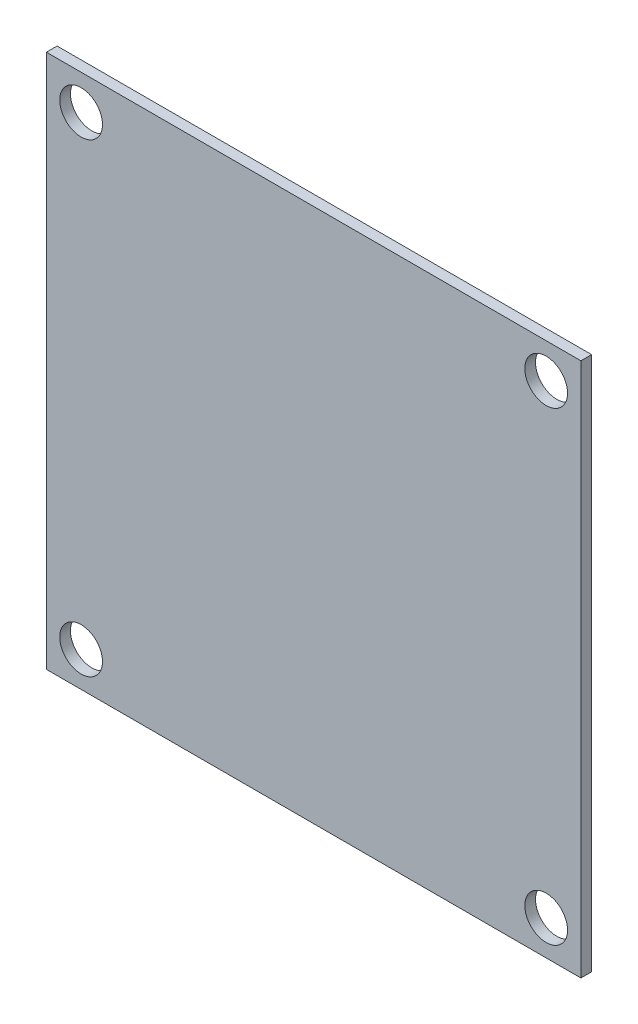
SolidWorks part; units mm, degrees
ref_plane "Front Plane" through (0, 0, 0) normal (0, 0, 1) x (1, 0, 0)
ref_plane "Top Plane" through (0, 0, 0) normal (0, 1, 0) x (1, 0, 0)
ref_plane "Right Plane" through (0, 0, 0) normal (1, 0, 0) x (0, 0, -1)
sketch "Sketch1" plane through (0, 0, 0) normal (0, 0, 1) x (1, 0, 0)
  line L1 (-20, 20) -> (20, 20)
  line L2 (-20, 20) -> (-20, -20)
  line L3 (-20, -20) -> (20, -20)
  line L4 (20, 20) -> (20, -20)
  line L5 (-20, 20) -> (20, -20) construction
  line L6 (-20, -20) -> (20, 20) construction
  point P0 (0, 0)
  dimension "D1" = 40
  dimension "D2" = 40
extrude "Boss-Extrude1" add sketch "Sketch1" along normal blind 0.8
sketch "Sketch2" plane through (0, 0, 0) normal (0, 0, 1) x (1, 0, 0)
  line L0 (-20, 20) -> (-20, -20) construction
  line L1 (-20, -20) -> (20, -20) construction
  line L2 (20, -20) -> (20, 20) construction
  line L3 (20, 20) -> (-20, 20) construction
  circle A0 centre (-17.4, -17.4) radius 1.6
  circle A1 centre (-17.4, 17.4) radius 1.6
  circle A2 centre (17.4, 17.4) radius 1.6
  circle A3 centre (17.4, -17.4) radius 1.6
  dimension "D1" = 2.6
  dimension "D2" = 2.6
  dimension "D3" = 2.6
  dimension "D4" = 2.6
extrude "Cut-Extrude1" cut sketch "Sketch2" along normal blind 0.8
